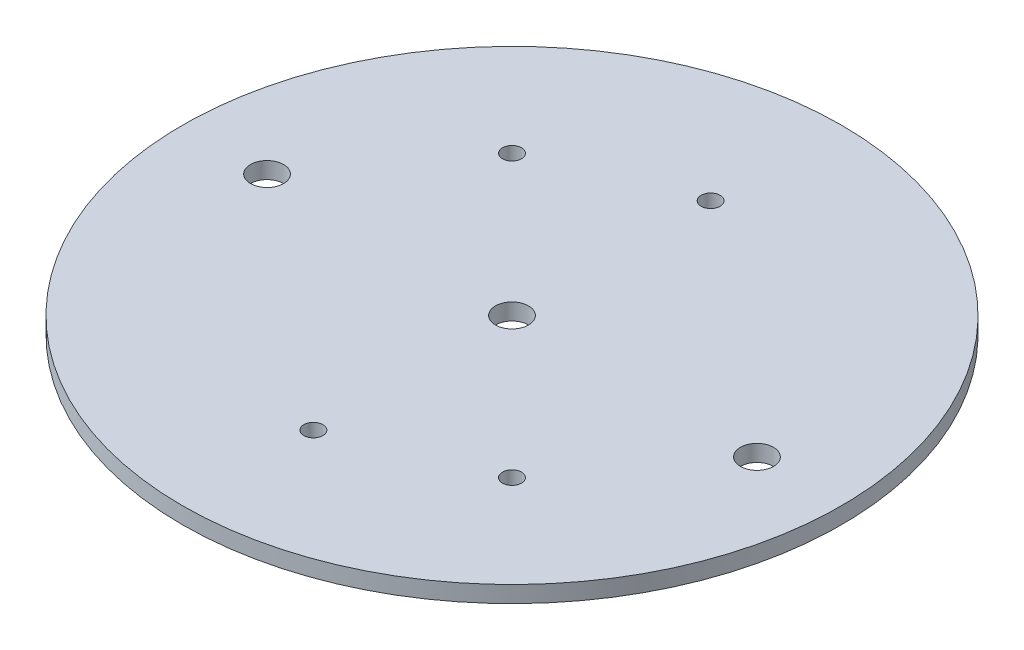
SolidWorks part; units mm, degrees
ref_plane "Front Plane" through (0, 0, 0) normal (0, 0, 1) x (1, 0, 0)
ref_plane "Top Plane" through (0, 0, 0) normal (0, 1, 0) x (1, 0, 0)
ref_plane "Right Plane" through (0, 0, 0) normal (1, 0, 0) x (0, 0, -1)
sketch "Sketch2" plane through (0, 0, 0) normal (0, 1, 0) x (1, 0, 0)
  line L0 (-46.99, 0) -> (46.99, 0) construction
  line L1 (0, -38.1) -> (0, 38.1) construction
  line L2 (-26.9408, 26.9408) -> (26.9408, -26.9408) construction
  circle A0 centre (0, 0) radius 63.2206
  circle A1 centre (-46.99, 0) radius 3.175
  circle A2 centre (46.99, 0) radius 3.175
  circle A3 centre (0, 0) radius 3.175
  circle A4 centre (0, 38.1) radius 1.8288
  circle A5 centre (0, -38.1) radius 1.8288
  circle A8 centre (-26.9408, 26.9408) radius 1.8288
  circle A9 centre (26.9408, -26.9408) radius 1.8288
  point P6 (0, 0)
  point P12 (0, 0)
  point P17 (0, 0)
  point P18 (0, 0)
  dimension "D1" = 126.4412
  dimension "D3" = 6.35
  dimension "D4" = 6.35
  dimension "D5" = 3.6576
  dimension "D6" = 76.2
  dimension "D8" = 45
  dimension "D7" = 76.2
  dimension "D2" = 93.98
extrude "Boss-Extrude1" add sketch "Sketch2" along normal blind 3.175
